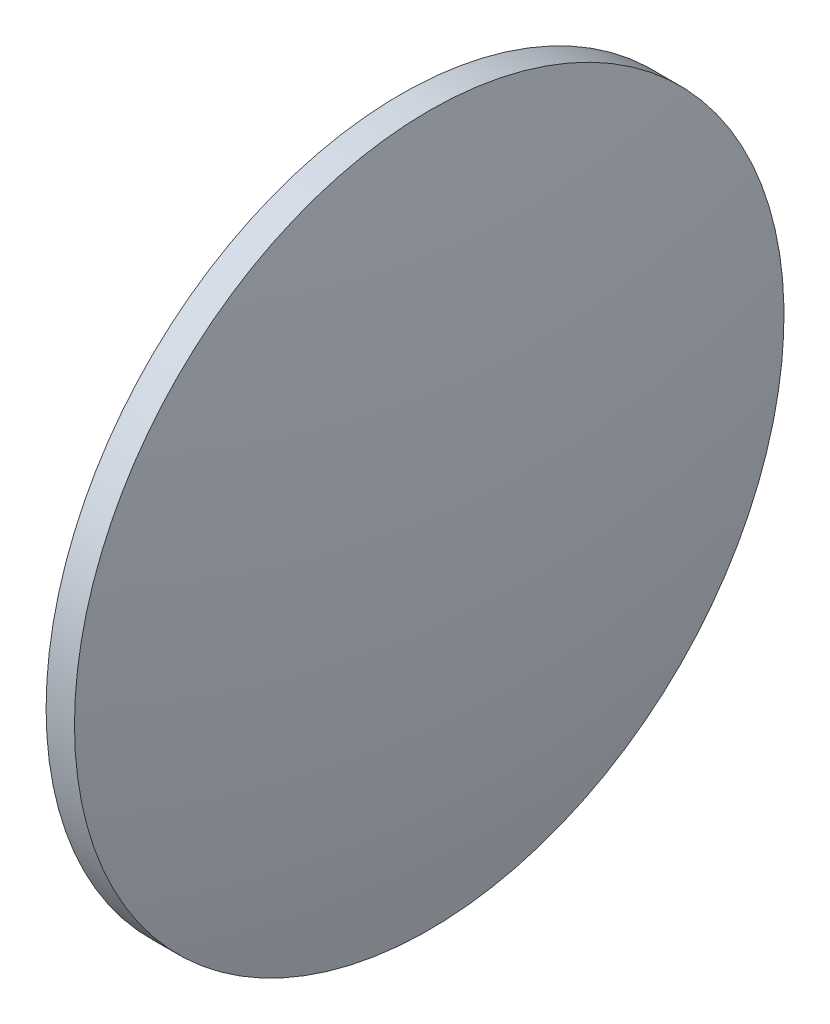
SolidWorks part; units mm, degrees
ref_plane "前视基准面" through (0, 0, 0) normal (0, 0, 1) x (1, 0, 0)
ref_plane "上视基准面" through (0, 0, 0) normal (0, 1, 0) x (1, 0, 0)
ref_plane "右视基准面" through (0, 0, 0) normal (1, 0, 0) x (0, 0, -1)
sketch "草图1" plane through (0, 0, 0) normal (0, 0, 1) x (1, 0, 0)
  line L0 (217.3311, 130.0419) -> (271.1141, 130.0419) construction
  line L1 (235.9389, 130.0419) -> (235.9389, 180.0419)
  line L2 (244.8289, 130.0419) -> (235.9389, 130.0419)
  line L5 (239.9389, 180.0419) -> (235.9389, 180.0419)
  arc A0 (244.8289, 130.0419) -> (239.9389, 180.0419) centre (-13.2398, 130.0419) ccw
revolve "旋转1" add sketch "草图1" angle 360 about L0
